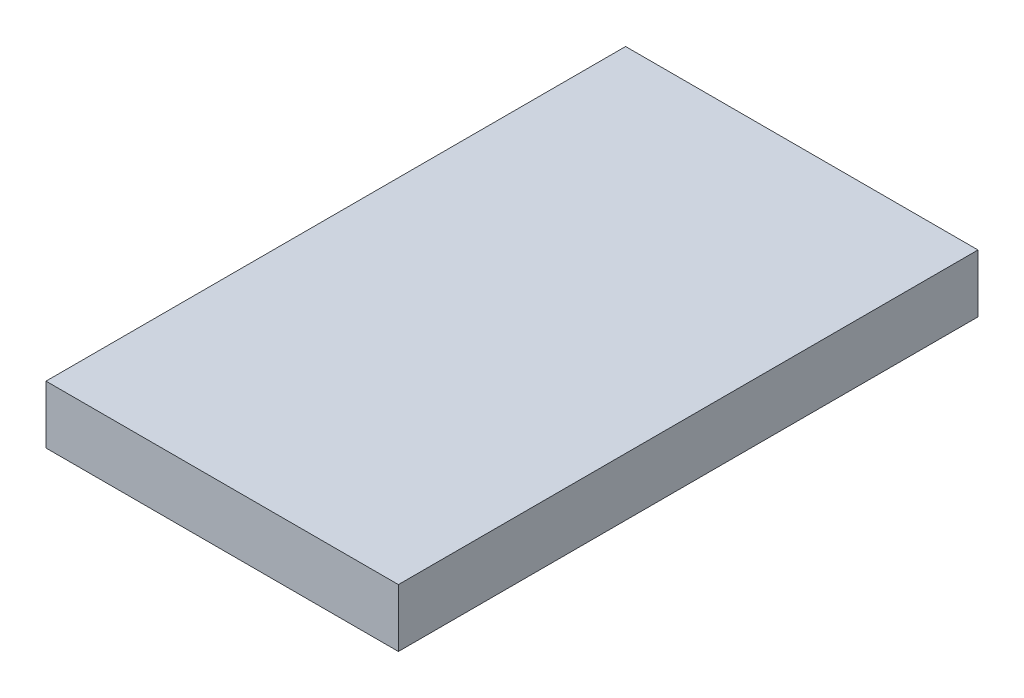
SolidWorks part; units mm, degrees
ref_plane "Ebene vorne" through (0, 0, 0) normal (0, 0, 1) x (1, 0, 0)
ref_plane "Ebene oben" through (0, 0, 0) normal (0, 1, 0) x (1, 0, 0)
ref_plane "Ebene rechts" through (0, 0, 0) normal (1, 0, 0) x (0, 0, -1)
sketch "Skizze1" plane through (0, 0, 0) normal (0, 0, 1) x (1, 0, 0)
  line L1 (-226.305, -17.025) -> (-220.225, -17.025)
  line L2 (-226.305, -17.025) -> (-226.305, -16.025)
  line L3 (-226.305, -16.025) -> (-220.225, -16.025)
  line L4 (-220.225, -17.025) -> (-220.225, -16.025)
  circle A0 centre (-225.805, -16.525) radius 0.5 construction
  circle A1 centre (-223.265, -16.525) radius 0.5 construction
  circle A2 centre (-220.725, -16.525) radius 0.5 construction
extrude "Aufsatz-Linear austragen1" add sketch "Skizze1" along normal blind 10
